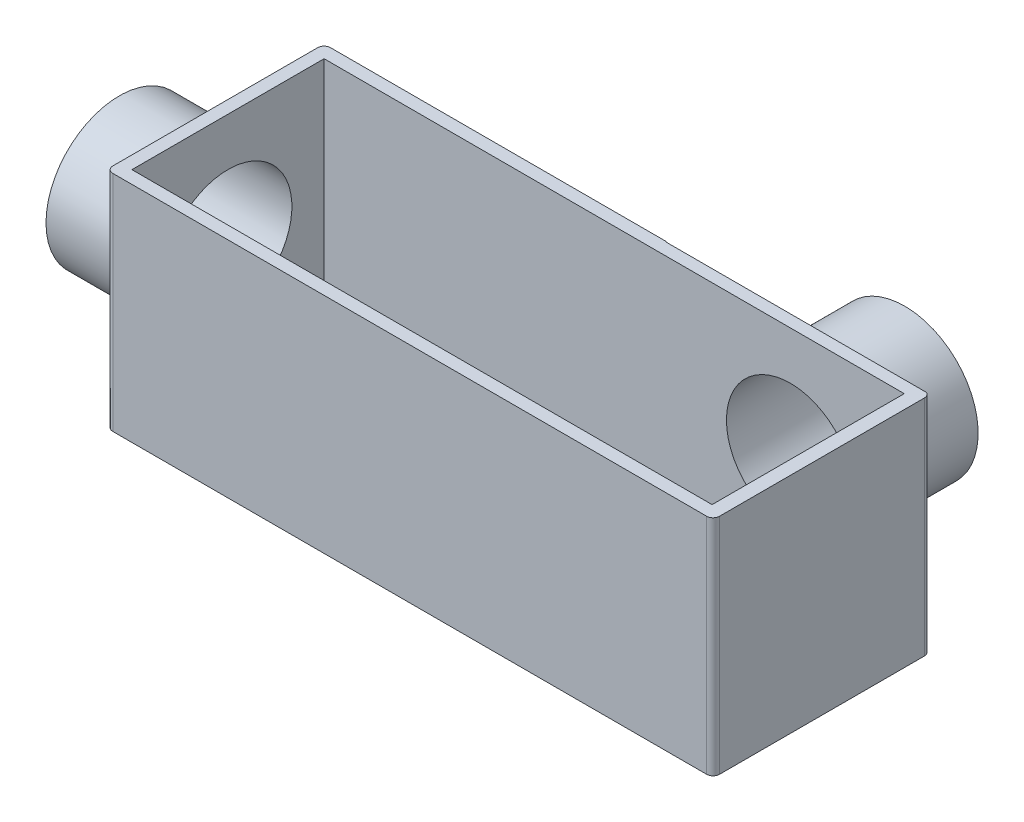
SolidWorks part; units mm, degrees
ref_plane "Alzado" through (0, 0, 0) normal (0, 0, 1) x (1, 0, 0)
ref_plane "Planta" through (0, 0, 0) normal (0, 1, 0) x (1, 0, 0)
ref_plane "Vista lateral" through (0, 0, 0) normal (1, 0, 0) x (0, 0, -1)
sketch "Croquis1" plane through (0, 0, 0) normal (0, 1, 0) x (1, 0, 0)
  line L0 (-55, -22.9545) -> (-55, 7.0455) construction
  line L1 (54, -25) -> (-39, -25)
  line L2 (55, -24) -> (55, 8.0909)
  line L3 (21, 25) -> (49, 25)
  line L7 (20, 10.0909) -> (20, 24)
  line L8 (50, 24) -> (50, 10.0909)
  line L9 (51, 9.0909) -> (54, 9.0909)
  line L10 (-55, -21.9545) -> (-55, 6.0455)
  line L11 (-40, 8.0455) -> (-40, 8.0909)
  line L12 (-39, 9.0909) -> (19, 9.0909)
  line L13 (-41, 7.0455) -> (-54, 7.0455)
  line L14 (-54, -22.9545) -> (-41, -22.9545)
  line L15 (-40, -23.9545) -> (-40, -24)
  arc A0 (-54, -22.9545) -> (-55, -21.9545) centre (-54, -21.9545) cw
  arc A1 (-54, 7.0455) -> (-55, 6.0455) centre (-54, 6.0455) ccw
  arc A2 (50, 24) -> (49, 25) centre (49, 24) ccw
  arc A3 (21, 25) -> (20, 24) centre (21, 24) ccw
  arc A4 (54, -25) -> (55, -24) centre (54, -24) ccw
  arc A5 (55, 8.0909) -> (54, 9.0909) centre (54, 8.0909) ccw
  arc A6 (51, 9.0909) -> (50, 10.0909) centre (51, 10.0909) cw
  arc A7 (19, 9.0909) -> (20, 10.0909) centre (19, 10.0909) ccw
  arc A8 (-39, 9.0909) -> (-40, 8.0909) centre (-39, 8.0909) ccw
  arc A9 (-39, -25) -> (-40, -24) centre (-39, -24) cw
  arc A10 (-40, -23.9545) -> (-41, -22.9545) centre (-41, -23.9545) ccw
  arc A11 (-40, 8.0455) -> (-41, 7.0455) centre (-41, 8.0455) cw
  point P0 (0, 0)
  point P16 (-55, -7.9545)
  point P25 (20, 25)
  point P34 (20, 9.0909)
  dimension "D3" = 1
  dimension "D1" = 15.9091
  dimension "D2" = 30
extrude "Saliente-Extruir1" add sketch "Croquis1" along normal blind 35
sketch "Croquis2" plane through (-55, 0, 0) normal (-1, 0, 0) x (0, 0, 1)
  line L0 (-6.0455, 17.5) -> (21.9545, 17.5) construction
  line L1 (-6.0455, 35) -> (-6.0455, 0) construction
  line L2 (21.9545, 35) -> (21.9545, 0) construction
  circle A0 centre (7.9545, 17.5) radius 11.5
  circle A1 centre (7.9545, 17.5) radius 23.9663
  dimension "D1" = 23
extrude "Cortar-Extruir1" cut sketch "Croquis2" against normal blind 15
sketch "Croquis3" plane through (0, 0, -25) normal (0, 0, -1) x (-1, 0, 0)
  line L0 (-21, 17.5) -> (-49, 17.5) construction
  line L1 (-21, 35) -> (-21, 0) construction
  line L2 (-49, 35) -> (-49, 0) construction
  circle A0 centre (-35, 17.5) radius 11.5
  circle A1 centre (-35, 17.5) radius 27.6597
  dimension "D1" = 23
extrude "Cortar-Extruir2" cut sketch "Croquis3" against normal blind 16
sketch "Croquis4" plane through (0, 35, 0) normal (0, 1, 0) x (1, 0, 0)
  line L0 (7.5, -25) -> (7.3403, 9.0909) construction
  line L1 (-39, -25) -> (54, -25) construction
  line L2 (13.5802, 9.0909) -> (-39, 9.0909) construction
  line L3 (52.8403, -23) -> (-38, -23)
  line L4 (52.8403, -23) -> (52.8403, 7.0909)
  line L5 (52.8403, 7.0909) -> (-38, 7.0909)
  line L6 (-38, -23) -> (-38, 7.0909)
  line L7 (52.8403, -23) -> (-38, 7.0909) construction
  line L8 (52.8403, 7.0909) -> (-38, -23) construction
  line L9 (-40, 3.5455) -> (-40, -19.4545) construction
  point P5 (7.4202, -7.9545)
  dimension "D1" = 2
  dimension "D2" = 2
extrude "Cortar-Extruir3" cut sketch "Croquis4" against normal blind 33
sketch "Croquis5" plane through (-55, 0, 0) normal (-1, 0, 0) x (0, 0, 1)
  circle A0 centre (7.9545, 17.5) radius 10
  dimension "D1" = 20
extrude "Cortar-Extruir5" cut sketch "Croquis5" against normal blind 33
sketch "Croquis6" plane through (0, 0, -25) normal (0, 0, -1) x (-1, 0, 0)
  circle A0 centre (-35, 17.5) radius 10
  dimension "D1" = 20
extrude "Cortar-Extruir6" cut sketch "Croquis6" against normal blind 33
